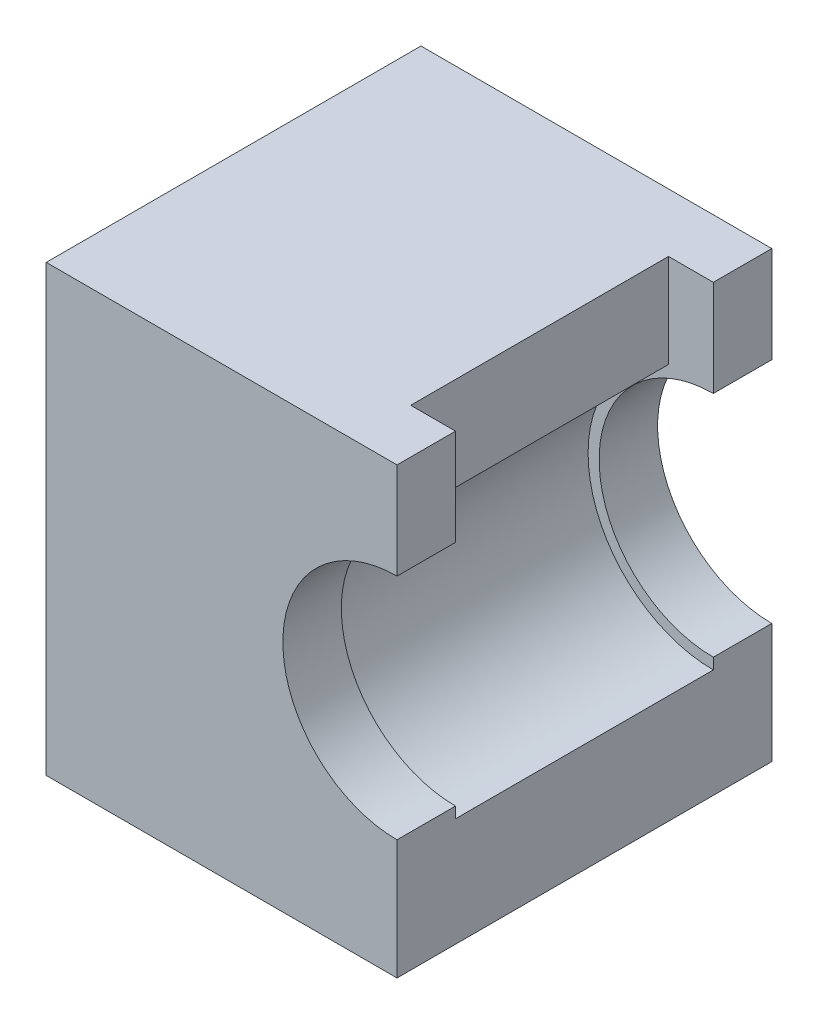
SolidWorks part; units mm, degrees
ref_plane "Front Plane" through (0, 0, 0) normal (0, 0, 1) x (1, 0, 0)
ref_plane "Top Plane" through (0, 0, 0) normal (0, 1, 0) x (1, 0, 0)
ref_plane "Right Plane" through (0, 0, 0) normal (1, 0, 0) x (0, 0, -1)
sketch "Sketch1" plane through (0, 0, 0) normal (0, 0, 1) x (1, 0, 0)
  line L0 (-9.2803, -6.35) -> (8.9621, -6.35) construction
  line L1 (-1.2163, 3.175) -> (-6.35, 3.175)
  line L2 (-6.35, 3.175) -> (-6.35, -6.35)
  line L3 (-6.35, -6.35) -> (0, -6.35)
  line L4 (0, -6.35) -> (0, -3.4)
  line L6 (-6.35, 3.175) -> (-9.525, 3.175)
  line L7 (-6.35, 3.175) -> (-6.35, -6.35)
  line L8 (-6.35, -6.35) -> (-9.525, -6.35)
  line L9 (-9.525, 3.175) -> (-9.525, -6.35)
  line L10 (-1.2163, 3.175) -> (-9.525, 3.175)
  line L11 (-1.2163, 3.175) -> (-1.2163, 5.715)
  line L12 (-1.2163, 5.715) -> (-9.525, 5.715)
  line L13 (-9.525, 3.175) -> (-9.525, 5.715)
  circle A0 centre (0, 0) radius 3.4
  dimension "D1" = 3.175
  dimension "D4" = 6.8
  dimension "D2" = 6.35
  dimension "D3" = 0
  dimension "D5" = 3.175
  dimension "D6" = 6.35
  dimension "D7" = 2.54
extrude "Boss-Extrude1" add sketch "Sketch1" along normal blind 7 contours A0 L1 L2 L3 L4 | L7 L6 L9 L8 | L11 L10 L13 L12
ref_plane "Plane1" through (0, 0, 3.5) normal (0, 0, 1) x (1, 0, 0)
sketch "Sketch2" plane through (0, 0, 7) normal (0, 0, 1) x (1, 0, 0)
  line L1 (-1.2163, 5.715) -> (0, 5.715)
  line L2 (-1.2163, 5.715) -> (-1.2163, -6.35)
  line L3 (-1.2163, -6.35) -> (0, -6.35)
  line L4 (0, 5.715) -> (0, -6.35)
  line L5 (-1.2163, 5.715) -> (-9.525, 5.715)
  line L6 (-9.525, 5.715) -> (-9.525, -6.35)
  line L7 (-9.525, -6.35) -> (0, -6.35)
  line L8 (0, -6.35) -> (0, -3.4)
  line L9 (-1.2163, 3.175) -> (-1.2163, 5.715)
  line L10 (-1.2163, 5.715) -> (-9.525, 5.715)
  line L11 (-9.525, 5.715) -> (-9.525, -6.35)
  line L12 (-9.525, -6.35) -> (0, -6.35)
  line L13 (0, -6.35) -> (0, -3.4)
  line L14 (-1.2163, 3.175) -> (-1.2163, 5.715)
  circle A0 centre (0, 0) radius 3.1
  arc A1 (-1.2163, 3.175) -> (0, -3.4) centre (0, 0) ccw
  arc A2 (-1.2163, 3.175) -> (0, -3.4) centre (0, 0) ccw
  line M7 (-1.2163, 5.715) -> (-9.525, 5.715)
  line M8 (-9.525, 5.715) -> (-9.525, -6.35)
  line M9 (-9.525, -6.35) -> (0, -6.35)
  line M10 (0, -6.35) -> (0, -3.4)
  arc M11 (0, -3.4) -> (-1.2163, 3.175) centre (0, 0) cw
  line M12 (-1.2163, 3.175) -> (-1.2163, 5.715)
  dimension "D2" = 6.2
  dimension "D1" = 0
extrude "Boss-Extrude2" add sketch "Sketch2" along normal blind 1.5875 contours L2 M11 M12 M7 M8 M9 | A0 L2 M11 | A0 L2 L4 M11 | L2 M11 M9 M10 | A0 L4 L1 L2 M12
mirror "Mirror1" about plane through (0, 0, 3.5) normal (0, 0, 1) of "Boss-Extrude2"
